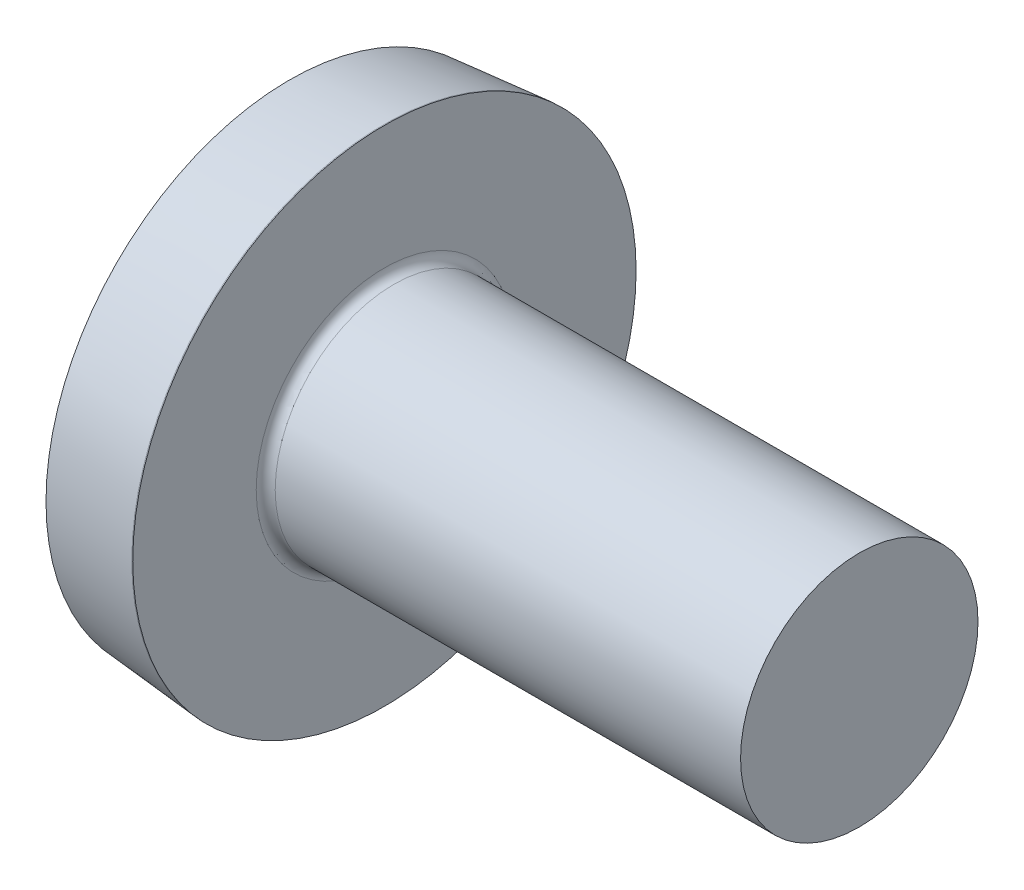
SolidWorks part; units mm, degrees
material "ABS"
ref_plane "Plane1" through (0, 0, 0) normal (0, 0, 1) x (1, 0, 0)
ref_plane "Plane2" through (0, 0, 0) normal (0, 1, 0) x (1, 0, 0)
ref_plane "Plane3" through (0, 0, 0) normal (1, 0, 0) x (0, 0, -1)
sketch "BodySke" plane through (0, 0, 0) normal (0, 0, 1) x (1, 0, 0)
  line L0 (1.5, 1.25) -> (1.5, 2.65)
  line L1 (1.95, 6.35) -> (1.95, -3.175) construction
  line L2 (-25.4, 0) -> (127, 0) construction
  line L3 (6.5, 0) -> (0, 0)
  line L4 (1.5, 1.25) -> (6.5, 1.25)
  line L5 (6.5, 1.25) -> (6.5, 0)
  line L6 (0.5, 2.5634) -> (1.49, 2.65)
  line L8 (1.5, 6.35) -> (1.5, -3.175) construction
  line L9 (1.5, 2.65) -> (1.49, 2.65)
  arc A0 (0.5, 2.5634) -> (0, 0) centre (6.8209, 0) ccw
  dimension "Length" = 5
  dimension "Head_ht" = 1.5
  dimension "Advance" = 0.45
  dimension "Thread_nom" = 5
  dimension "Diameter" = 2.5
  dimension "Head_dia" = 5.3
  dimension "Head_ang" = 85
  dimension "Oval_ht" = 0.5
  dimension "D1" = 0.01
revolve "Base-Revolve" add sketch "BodySke"
cosmetic thread "ThreadCosmetic" [suppressed]
fillet "Fillet1" radius 0.1 1 edges at (1.5, 0, 1.25)
sketch "Sketch3" plane through (0, 0, 0) normal (1, 0, 0) x (0, 0, -1)
  line L0 (0.37, -1.25) -> (-0.37, -1.25)
  line L1 (0.37, -1.25) -> (0.37, 1.25)
  line L2 (-0.37, 1.25) -> (0.37, 1.25)
  line L3 (-0.37, 1.25) -> (-0.37, -1.25)
  dimension "Cross_dia" = 2.5
  dimension "D1" = 1.25
  dimension "Cross_width" = 0.74
  dimension "D2" = 0.37
ref_plane "Plane4" through (1.32, 0, 0) normal (1, 0, 0) x (0, 0, -1)
sketch "Sketch4" plane through (1.32, 0, 0) normal (1, 0, 0) x (0, 0, -1)
  line L0 (0.37, -0.5919) -> (-0.37, -0.5919)
  line L1 (0.37, -0.5919) -> (0.37, 0.5919)
  line L2 (-0.37, 0.5919) -> (0.37, 0.5919)
  line L3 (-0.37, 0.5919) -> (-0.37, -0.5919)
  dimension "D1" = 0.74
  dimension "D2" = 1.1837
  dimension "D3" = 0.37
  dimension "D4" = 0.5919
loft "Recess" cut profiles "Sketch3", "Sketch4"
pattern_circular "RecPat" count 2 every 90 about axis through (0, 0, 0) along (1, 0, 0) of "Recess"
sketch "RecCorSke" plane through (0, 0, 0) normal (0, 0, 1) x (1, 0, 0)
  line L0 (-3.175, 0) -> (15.875, 0) construction
  line L1 (-25.4, 0) -> (127, 0) construction
  line L2 (0, 0) -> (0, 0.6483)
  line L3 (0, 0.6483) -> (1.32, 0.556)
  line L4 (1.32, 0.556) -> (1.5007, 0)
  line L5 (1.5007, 0) -> (0, 0)
  dimension "Diameter" = 1.112
  dimension "Depth" = 1.32
  dimension "Draft_angle" = 4
  dimension "Bottom_angle" = 18
revolve "RecessCore" cut sketch "RecCorSke" angle 360 about L0
sketch "ThdSchSke" plane through (0, 0, 0) normal (0, 0, 1) x (1, 0, 0)
  line L0 (2.4, -0.9965) -> (2.2225, -1.25)
  line L1 (2.4, -0.9965) -> (2.5775, -1.25)
  line L2 (2.5775, -1.25) -> (2.5775, -1.5625)
  line L3 (-3.175, 0) -> (5.1513, 0) construction
  line L5 (2.5775, -1.5625) -> (2.2225, -1.5625)
  line L6 (2.2225, -1.5625) -> (2.2225, -1.25)
  dimension "Diameter" = 2.5
  dimension "SideAngle" = 55
  dimension "VeeAngle" = 70
  dimension "Thread_minor" = 1.993
  dimension "Overcut" = 3.125
  dimension "Start" = 2.4
revolve "ThreadSchematic" [suppressed] cut sketch "ThdSchSke" angle 360 about L3
pattern_linear "ThdSchPat" [suppressed]
equation "' \"Diameter@BodySke\" = 8"
equation "' \"Length@BodySke\" = 35"
equation "' \"Head_dia@BodySke\" = 16.4"
equation "' \"Oval_ht@BodySke\" = 1.7"
equation "' \"Head_ht@BodySke\" = 4.8"
equation "' \"Thread_nom@BodySke\" =  30"
equation "' \"Thread_nom@BodySke\" = 30"
equation "' \"Head_ang@BodySke\" = 85"
equation "' \"Cross_dia@Sketch3\" = 7.8"
equation "' \"Cross_width@Sketch3\" = 1.42"
equation "' \"Cross_depth@Plane4\" = 4.36"
equation "' \"Diameter@RecCorSke\" = 2.561"
equation "' \"Radius@Fillet1\" = 0.4"
equation "' \"Thread_minor@ThreadCosmetic\" = 6.619"
equation "' \"Advance@BodySke\" = 1.25"
equation "\"D1@Sketch3\" = \"Cross_dia@Sketch3\" / 2"
equation "\"D2@Sketch3\" = \"Cross_width@Sketch3\" / 2"
equation "\"Depth@RecCorSke\" = \"Cross_depth@Plane4\""
equation "\"D1@Sketch4\" = \"Cross_width@Sketch3\""
equation "\"D2@Sketch4\" = \"Cross_dia@Sketch3\" - 2.0 * \"Cross_depth@Plane4\" * tan(26.5  * 0.017453292)"
equation "\"D3@Sketch4\" = \"D1@Sketch4\" / 2"
equation "\"D4@Sketch4\" = \"D2@Sketch4\" / 2"
equation "\"Thread_length@ThreadCosmetic\" = ((sgn( (\"Length@BodySke\" - \"Advance@BodySke\" * 2.0 ) - \"Thread_nom@BodySke\" )-1)*( (\"Length@BodySke\" - \"Advance@BodySke\" * 2.0 ) - \"Thread_nom@BodySke\" ))/-2+ \"Thread_nom@BodySke\""
equation "\"Thread_minor@ThdSchSke\" = \"Thread_minor@ThreadCosmetic\""
equation "\"Diameter@ThdSchSke\" = \"Diameter@BodySke\""
equation "\"Overcut@ThdSchSke\" = \"Diameter@BodySke\" * 1.25"
equation "\"Start@ThdSchSke\" = \"Head_ht@BodySke\" + \"Length@BodySke\" - \"Thread_length@ThreadCosmetic\"  '---Non-countersunk---"
equation "\"Num_threads@ThdSchPat\" = int( \"Thread_length@ThreadCosmetic\" / \"Advance@BodySke\" + 0.999 )  + 1"
equation "\"Advance@ThdSchPat\" = \"Thread_length@ThreadCosmetic\" /  (\"Num_threads@ThdSchPat\" - 1) 'relax it"
